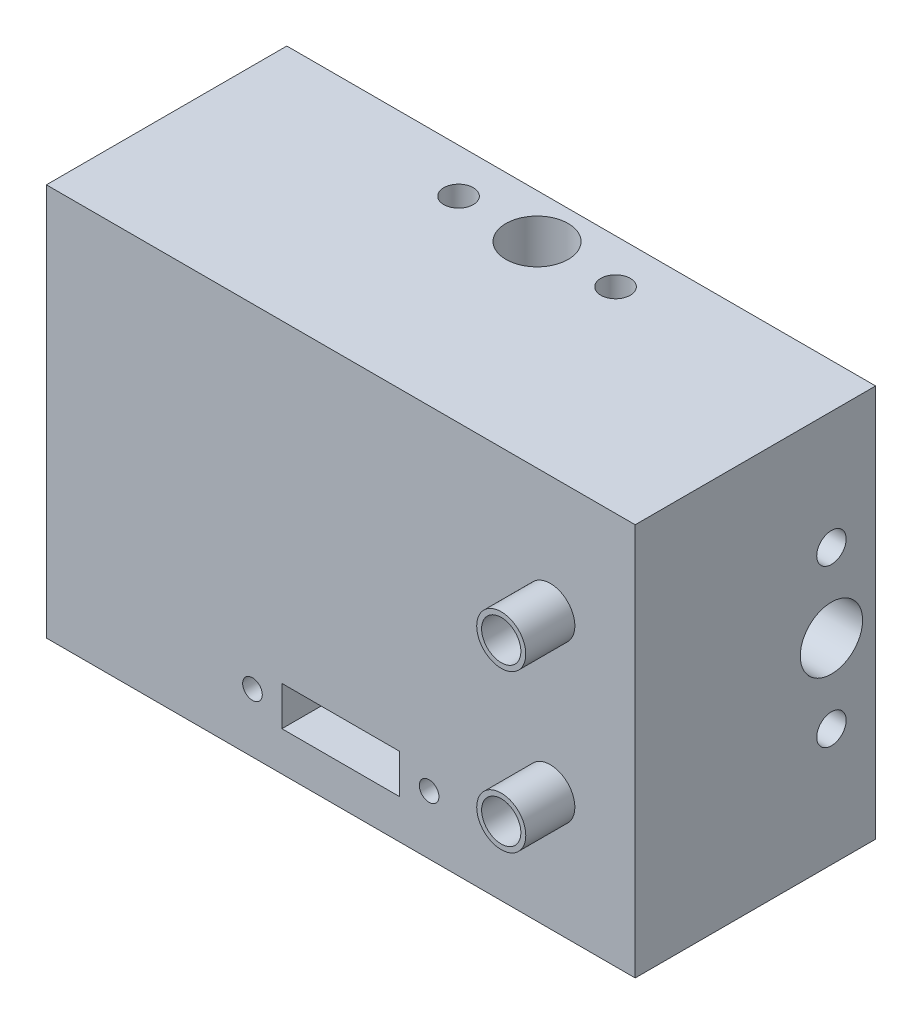
SolidWorks part; units mm, degrees
ref_plane "Front Plane" through (0, 0, 0) normal (0, 0, 1) x (1, 0, 0)
ref_plane "Top Plane" through (0, 0, 0) normal (0, 1, 0) x (1, 0, 0)
ref_plane "Right Plane" through (0, 0, 0) normal (1, 0, 0) x (0, 0, -1)
sketch "Sketch1" plane through (0, 0, 0) normal (0, 0, 1) x (1, 0, 0)
  line L1 (0, 0) -> (60, 0)
  line L2 (0, 0) -> (0, 40)
  line L3 (0, 40) -> (60, 40)
  line L4 (60, 0) -> (60, 40)
  dimension "D1" = 60
  dimension "D2" = 40
extrude "Boss-Extrude1" add sketch "Sketch1" along normal blind 24.5
sketch "Sketch2" plane through (0, 0, 0) normal (0, 0, -1) x (-1, 0, 0)
  line L0 (-30, 40) -> (-30, 0) construction
  line L1 (-60, 40) -> (0, 40) construction
  line L2 (0, 0) -> (-60, 0) construction
  circle A0 centre (-30, 20) radius 15
  circle A1 centre (-30, 20) radius 14
  dimension "D1" = 30
  dimension "D2" = 1
extrude "Boss-Extrude2" add sketch "Sketch2" along normal blind 1
sketch "Sketch3" plane through (0, 0, 0) normal (-1, 0, 0) x (0, 0, 1)
  line L0 (4.5, 40) -> (4.5, 0) construction
  line L1 (24.5, 40) -> (0, 40) construction
  line L2 (24.5, 0) -> (0, 0) construction
  line L3 (0, 40) -> (0, 0) construction
  line L4 (0, 20) -> (24.5, 20) construction
  line L5 (24.5, 40) -> (24.5, 0) construction
  circle A0 centre (4.5, 20) radius 3.175
  circle A1 centre (4.5, 28) radius 1.5
  circle A2 centre (4.5, 12) radius 1.5
  dimension "D2" = 6.35
  dimension "D3" = 3
  dimension "D1" = 4.5
  dimension "D4" = 8
extrude "Cut-Extrude1" cut sketch "Sketch3" against normal blind 10
ref_point "Point1"
ref_plane "Plane1" through (30, 0, 0) normal (1, 0, 0) x (0, 0, -1)
mirror "Mirror1" about plane through (30, 0, 0) normal (1, 0, 0) of "Cut-Extrude1"
sketch "Sketch4" plane through (0, 40, 0) normal (0, 1, 0) x (1, 0, 0)
  line L0 (0, -4.5) -> (60, -4.5) construction
  line L1 (0, -24.5) -> (0, 0) construction
  line L2 (60, -24.5) -> (60, 0) construction
  line L4 (60, 0) -> (0, 0) construction
  line L5 (30, 0) -> (30, -24.5) construction
  line L6 (60, -24.5) -> (0, -24.5) construction
  circle A0 centre (30, -4.5) radius 3.175
  circle A1 centre (38, -4.5) radius 1.5
  circle A2 centre (22, -4.5) radius 1.5
  dimension "D2" = 6.35
  dimension "D3" = 3
  dimension "D1" = 4.5
  dimension "D4" = 8
extrude "Cut-Extrude2" cut sketch "Sketch4" against normal blind 10
ref_point "Point2"
ref_plane "Plane3" through (0, 20, 0) normal (0, -1, 0) x (-1, 0, 0)
mirror "Mirror2" about plane through (0, 20, 0) normal (0, -1, 0) of "Cut-Extrude2"
sketch "Sketch5" plane through (0, 0, 24.5) normal (0, 0, 1) x (1, 0, 0)
  line L0 (30, 0) -> (30, 40) construction
  line L5 (0, 0) -> (60, 0) construction
  line L6 (60, 40) -> (0, 40) construction
  line L8 (24, 4) -> (36, 4)
  line L9 (24, 4) -> (24, 8)
  line L10 (24, 8) -> (36, 8)
  line L11 (36, 4) -> (36, 8)
  line L12 (24, 4) -> (36, 8) construction
  line L13 (24, 8) -> (36, 4) construction
  circle A0 centre (21, 6) radius 1
  circle A1 centre (39, 6) radius 1
  point P0 (30, 6)
  point P13 (0, 0)
  point P14 (0, 0)
  point P15 (21, 6)
  point P16 (21, 6)
  dimension "D4" = 2
  dimension "D1" = 6
  dimension "D2" = 4
  dimension "D3" = 12
  dimension "D5" = 9
extrude "Cut-Extrude3" cut sketch "Sketch5" against normal blind 5
sketch "Sketch6" plane through (0, 0, 24.5) normal (0, 0, 1) x (1, 0, 0)
  line L0 (51.35, 40) -> (51.35, 0) construction
  line L1 (60, 40) -> (0, 40) construction
  line L2 (0, 0) -> (60, 0) construction
  line L3 (60, 0) -> (60, 40) construction
  line L4 (0, 20) -> (60, 20) construction
  line L5 (0, 40) -> (0, 0) construction
  circle A0 centre (51.35, 12) radius 2
  circle A1 centre (51.35, 12) radius 2.5
  circle A2 centre (51.35, 28) radius 2.5
  circle A3 centre (51.35, 28) radius 2
  dimension "D2" = 4
  dimension "D1" = 8.65
  dimension "D3" = 0.5
  dimension "D4" = 16
extrude "Boss-Extrude4" add sketch "Sketch6" along normal blind 5
